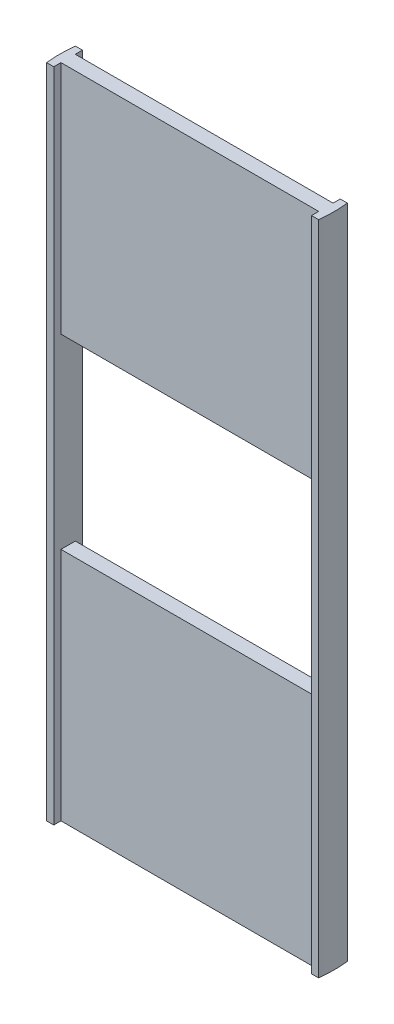
SolidWorks part; units mm, degrees
ref_plane "Front Plane" through (0, 0, 0) normal (0, 0, 1) x (1, 0, 0)
ref_plane "Top Plane" through (0, 0, 0) normal (0, 1, 0) x (1, 0, 0)
ref_plane "Right Plane" through (0, 0, 0) normal (1, 0, 0) x (0, 0, -1)
sketch "Sketch1" plane through (0, 0, 0) normal (0, 1, 0) x (1, 0, 0)
  circle A0 centre (0, 0) radius 95.25
extrude "Boss-Extrude1" add sketch "Sketch1" along normal blind 457.2
sketch "Sketch2" plane through (0, 457.2, 0) normal (0, 1, 0) x (1, 0, 0)
  line L0 (89.7236, 10) -> (89.7236, 5)
  line L1 (94.7236, 10) -> (89.7236, 10)
  line L5 (89.7236, -10) -> (94.7236, -10)
  line L6 (89.7236, 5) -> (-89.7236, 5)
  line L7 (89.7236, -4.8893) -> (-89.7236, -4.8893)
  line L8 (89.7236, -10) -> (89.7236, -4.8893)
  line L11 (-94.7236, 10) -> (-89.7236, 10)
  line L12 (-89.7236, 10) -> (-89.7236, 5)
  line L13 (-94.7236, -10) -> (-89.7236, -10)
  line L14 (-89.7236, -10) -> (-89.7236, -5.7009)
  circle A0 centre (0, 0) radius 95.25 construction
  arc A1 (94.7236, 10) -> (-94.7236, 10) centre (0, 0) ccw
  arc A2 (-94.7236, -10) -> (94.7236, -10) centre (0, 0) ccw
  dimension "D1" = 5
  dimension "D2" = 5
  dimension "D3" = 5
extrude "Cut-Extrude1" cut sketch "Sketch2" against normal blind 457.2 contours A1 L11 L12 L6 L0 L1
sketch "Sketch5" plane through (0, 457.2, 0) normal (0, 1, 0) x (1, 0, 0)
  line L1 (0, -5) -> (-89.7236, -5)
  line L2 (0, -5) -> (89.7236, -5)
  line L3 (89.7236, -5) -> (89.7236, -10)
  line L4 (-89.7236, -5) -> (-89.7236, -10)
  line L5 (-89.7236, -10) -> (-94.7236, -10)
  line L6 (94.7236, -10) -> (89.7236, -10)
  arc A0 (-94.7236, 10) -> (94.7236, 10) centre (0, 0) ccw construction
  arc A1 (-94.7236, -10) -> (94.7236, -10) centre (0, 0) ccw
extrude "Cut-Extrude2" cut sketch "Sketch5" against normal blind 457.2
sketch "Sketch7" plane through (0, 0, 0) normal (0, 0, 1) x (1, 0, 0)
  line L0 (0, 0) -> (0, 20)
  line L1 (0, 20) -> (79.72, 20)
  line L2 (0, 20) -> (-79.72, 20)
  line L3 (-79.72, 20) -> (-79.72, 437.2)
  line L4 (-79.72, 439.3686) -> (79.72, 439.3686)
  line L5 (79.72, 439.3686) -> (79.72, 20)
sketch "Sketch9" plane through (0, 0, 0) normal (0, 0, 1) x (1, 0, 0)
  line L0 (0, 0) -> (0, 228.6) construction
  line L2 (89.7236, 0) -> (89.7236, 457.2) construction
  line L3 (-89.7236, 163.7138) -> (89.7236, 163.7138)
  line L4 (-89.7236, 163.7138) -> (-89.7236, 293.4862)
  line L5 (-89.7236, 293.4862) -> (89.7236, 293.4862)
  line L6 (89.7236, 163.7138) -> (89.7236, 293.4862)
  line L7 (-89.7236, 163.7138) -> (89.7236, 293.4862) construction
  line L8 (-89.7236, 293.4862) -> (89.7236, 163.7138) construction
extrude "Cut-Extrude4" cut sketch "Sketch9" against normal through all and the other way through all
